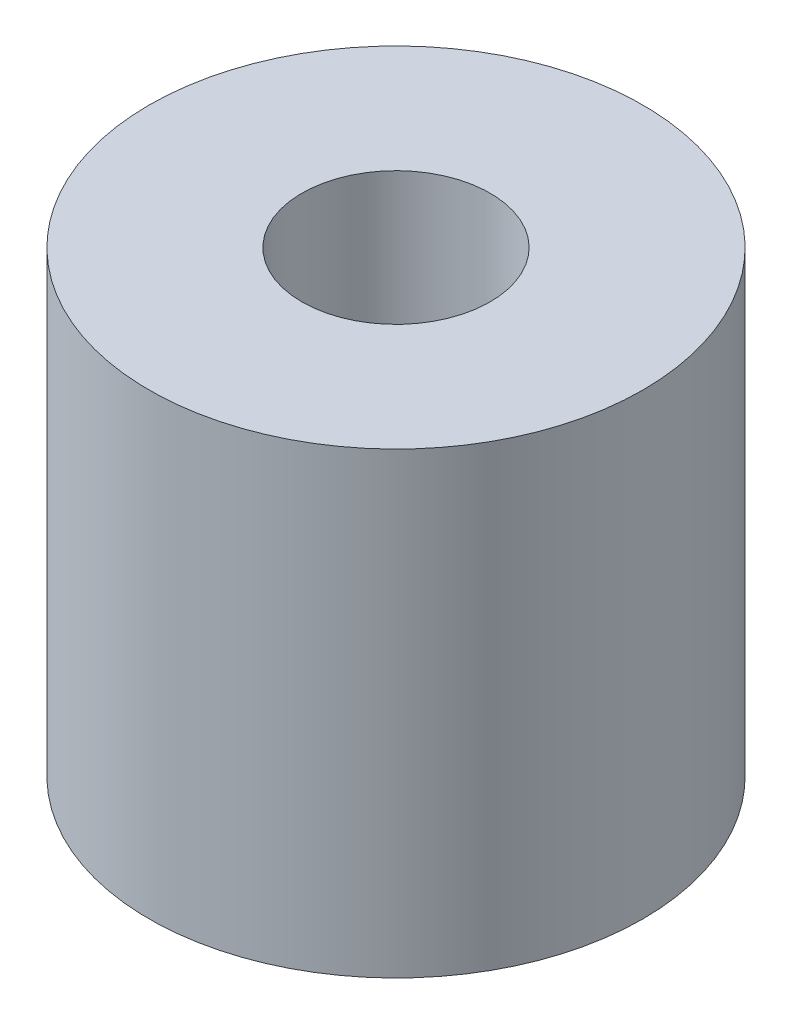
SolidWorks part; units mm, degrees
ref_plane "前视基准面" through (0, 0, 0) normal (0, 0, 1) x (1, 0, 0)
ref_plane "上视基准面" through (0, 0, 0) normal (0, 1, 0) x (1, 0, 0)
ref_plane "右视基准面" through (0, 0, 0) normal (1, 0, 0) x (0, 0, -1)
other "Configuration Table"
sketch "草图1" plane through (0, 0, 0) normal (0, 1, 0) x (1, 0, 0)
  circle A0 centre (0, 0) radius 1.85
  dimension "D1" = 3.7
extrude "拉伸-薄壁1" add sketch "草图1" along normal blind 9 thin
